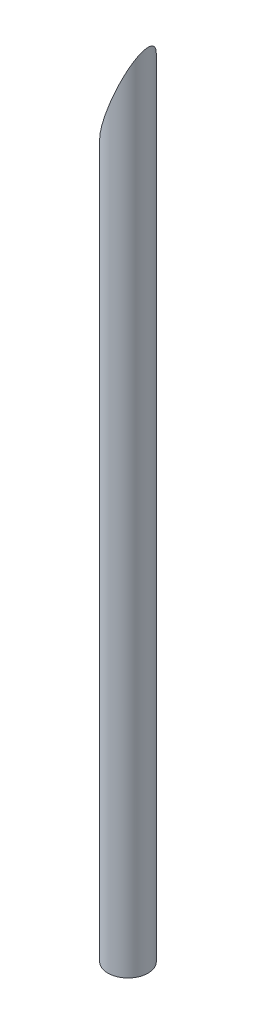
SolidWorks part; units mm, degrees
ref_plane "前视基准面" through (0, 0, 0) normal (0, 0, 1) x (1, 0, 0)
ref_plane "上视基准面" through (0, 0, 0) normal (0, 1, 0) x (1, 0, 0)
ref_plane "右视基准面" through (0, 0, 0) normal (1, 0, 0) x (0, 0, -1)
sketch "草图1" plane through (0, 0, 0) normal (0, 1, 0) x (1, 0, 0)
  circle A0 centre (0, 0) radius 0.15
  dimension "D1" = 0.3
extrude "凸台-拉伸1" add sketch "草图1" along normal blind 6
sketch "草图2" plane through (0, 0, 0) normal (0, 0, 1) x (1, 0, 0)
  line L0 (0.15, 6) -> (-0.15, 5.219)
  line L1 (-0.15, 6) -> (-0.15, 0) construction
  line L2 (-0.15, 5.219) -> (-0.15, 6)
  line L3 (-0.15, 6) -> (0.15, 6)
extrude "切除-拉伸1" cut sketch "草图2" against normal mid plane 6
